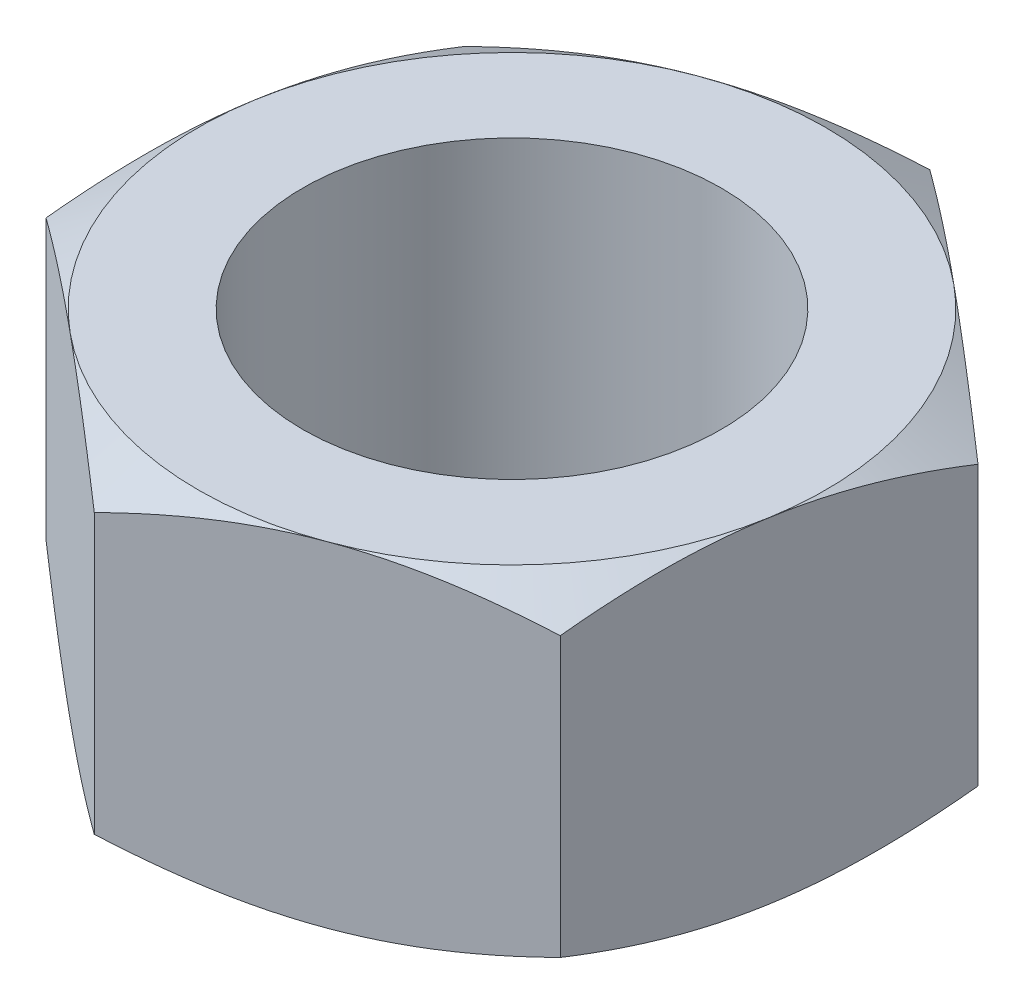
SolidWorks part; units mm, degrees
ref_plane "Front Plane" through (0, 0, 0) normal (0, 0, 1) x (1, 0, 0)
ref_plane "Top Plane" through (0, 0, 0) normal (0, 1, 0) x (1, 0, 0)
ref_plane "Right Plane" through (0, 0, 0) normal (1, 0, 0) x (0, 0, -1)
sketch "Sketch1" plane through (0, 0, 0) normal (0, 1, 0) x (1, 0, 0)
  line L1 (6.6732, -5.5198) -> (8.1169, 3.0193)
  line L2 (8.1169, 3.0193) -> (1.4437, 8.5391)
  line L3 (1.4437, 8.5391) -> (-6.6732, 5.5198)
  line L4 (-6.6732, 5.5198) -> (-8.1169, -3.0193)
  line L5 (-8.1169, -3.0193) -> (-1.4437, -8.5391)
  line L6 (-1.4437, -8.5391) -> (6.6732, -5.5198)
  circle A0 centre (0, 0) radius 7.5 construction
  dimension "D1" = 15
extrude "Boss-Extrude1" add sketch "Sketch1" along normal blind 8
sketch "Sketch7" plane through (0, 8, 0) normal (0, 1, 0) x (1, 0, 0)
  circle A0 centre (0, 0) radius 7.5
extrude "Cut-Extrude4" cut sketch "Sketch7" against normal blind 1 draft 60 flip side to cut
sketch "Sketch8" plane through (0, 0, 0) normal (0, -1, 0) x (1, 0, 0)
  circle A0 centre (0, 0) radius 7.5
extrude "Cut-Extrude5" cut sketch "Sketch8" against normal blind 1 draft 60 flip side to cut
sketch "Sketch9" plane through (0, 8, 0) normal (0, 1, 0) x (1, 0, 0)
  circle A0 centre (0, 0) radius 5
  dimension "D1" = 10
extrude "Cut-Extrude6" cut sketch "Sketch9" against normal blind 10
